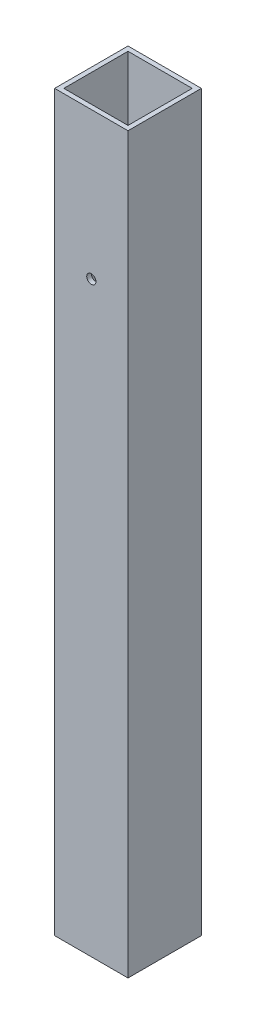
SolidWorks part; units mm, degrees
ref_plane "Front Plane" through (0, 0, 0) normal (0, 0, 1) x (1, 0, 0)
ref_plane "Top Plane" through (0, 0, 0) normal (0, 1, 0) x (1, 0, 0)
ref_plane "Right Plane" through (0, 0, 0) normal (1, 0, 0) x (0, 0, -1)
sketch "Sketch3" plane through (0, 0, 0) normal (0, 1, 0) x (1, 0, 0)
  line L0 (-11.1125, -11.1125) -> (-11.1125, 11.1125)
  line L1 (12.7, -12.7) -> (-12.7, -12.7)
  line L2 (12.7, -12.7) -> (12.7, 12.7)
  line L3 (12.7, 12.7) -> (-12.7, 12.7)
  line L4 (-12.7, -12.7) -> (-12.7, 12.7)
  line L5 (12.7, -12.7) -> (-12.7, 12.7) construction
  line L6 (12.7, 12.7) -> (-12.7, -12.7) construction
  line L11 (11.1125, 11.1125) -> (-11.1125, 11.1125)
  line L12 (11.1125, -11.1125) -> (11.1125, 11.1125)
  line L21 (11.1125, -11.1125) -> (-11.1125, -11.1125)
  point P0 (0, 0)
  dimension "D1" = 25.4
  dimension "D2" = 1.5875
extrude "Boss-Extrude1" add sketch "Sketch3" along normal blind 254
sketch "Sketch4" plane through (0, 0, 12.7) normal (0, 0, 1) x (1, 0, 0)
  line L0 (0, 254) -> (0, 0) construction
  line L1 (-12.7, 254) -> (12.7, 254) construction
  circle A0 centre (0, 203.2) radius 1.5875
  dimension "D1" = 3.175
  dimension "D2" = 50.8
extrude "Cut-Extrude1" cut sketch "Sketch4" against normal through all contours A0
